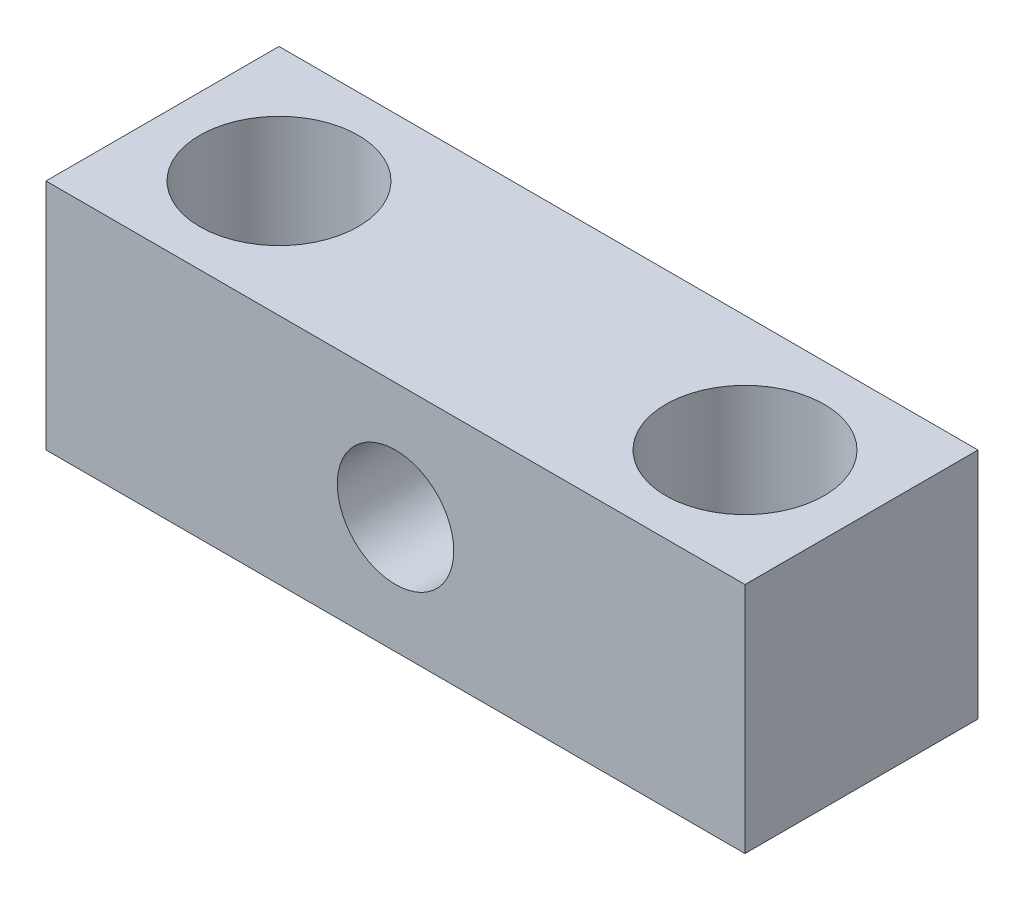
SolidWorks part; units mm, degrees
ref_plane "Alzado" through (0, 0, 0) normal (0, 0, 1) x (1, 0, 0)
ref_plane "Planta" through (0, 0, 0) normal (0, 1, 0) x (1, 0, 0)
ref_plane "Vista lateral" through (0, 0, 0) normal (1, 0, 0) x (0, 0, -1)
sketch "Croquis1" plane through (0, 0, 0) normal (0, 1, 0) x (1, 0, 0)
  line L5 (-2.5, -2.5) -> (2.5, 2.5) construction
  line L6 (-2.5, 2.5) -> (2.5, -2.5) construction
  line L7 (-7.5, -2.5) -> (7.5, -2.5)
  line L8 (-7.5, -2.5) -> (-7.5, 2.5)
  line L9 (-7.5, 2.5) -> (7.5, 2.5)
  line L10 (7.5, -2.5) -> (7.5, 2.5)
  line L11 (-7.5, -2.5) -> (7.5, 2.5) construction
  line L12 (-7.5, 2.5) -> (7.5, -2.5) construction
  point P0 (0, 0)
  point P5 (0, 0)
extrude "Saliente-Extruir1" add sketch "Croquis1" along normal blind 5
sketch "Croquis2" plane through (0, 5, 0) normal (0, 1, 0) x (1, 0, 0)
  line L0 (0, 0) -> (-7.5, 0) construction
  line L1 (-7.5, 2.5) -> (-7.5, -2.5) construction
  line L2 (-7.5, 0) -> (-5, 0) construction
  line L3 (-5, 0) -> (5, 0) construction
  line L4 (5, 0) -> (7.5, 0) construction
  line L5 (7.5, -2.5) -> (7.5, 2.5) construction
  circle A0 centre (-5, 0) radius 1.7
  circle A1 centre (5, 0) radius 1.7
extrude "Cortar-Extruir1" cut sketch "Croquis2" against normal through all
sketch "Croquis3" plane through (0, 0, 2.5) normal (0, 0, 1) x (1, 0, 0)
  line L0 (0, 0) -> (0, 2.5) construction
  line L1 (-7.5, 0) -> (7.5, 0) construction
  circle A0 centre (0, 2.5) radius 1.25
extrude "Cortar-Extruir2" cut sketch "Croquis3" against normal through all
